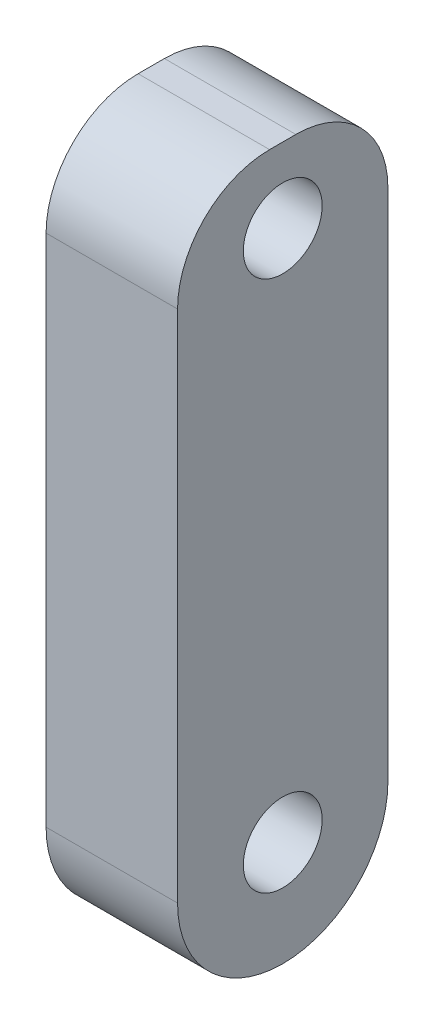
SolidWorks part; units mm, degrees
ref_plane "Front Plane" through (0, 0, 0) normal (0, 0, 1) x (1, 0, 0)
ref_plane "Top Plane" through (0, 0, 0) normal (0, 1, 0) x (1, 0, 0)
ref_plane "Right Plane" through (0, 0, 0) normal (1, 0, 0) x (0, 0, -1)
sketch "Sketch1" plane through (0, 0, 0) normal (1, 0, 0) x (0, 0, -1)
  line L0 (-21.5485, -38.9001) -> (108.4515, -38.9001) construction
  line L1 (44.1626, 9.8261) -> (44.1626, 29.3921)
  line L2 (47.6626, 32.8921) -> (48.6626, 32.8921)
  line L3 (52.1626, 29.3921) -> (52.1626, 9.8261)
  circle A0 centre (48.1626, 9.8261) radius 1.5
  circle A1 centre (48.1626, 9.8261) radius 4
  circle A2 centre (48.1626, 30.0515) radius 1.5
  arc A3 (52.1626, 29.3921) -> (48.6626, 32.8921) centre (48.6626, 29.3921) ccw
  arc A4 (44.1626, 29.3921) -> (47.6626, 32.8921) centre (47.6626, 29.3921) cw
  dimension "D2" = 3
  dimension "D3" = 8
  dimension "D4" = 3
  dimension "D5" = 3.5
  dimension "D1" = 130
extrude "Boss-Extrude1" add sketch "Sketch1" along normal blind 5 contours A1 A0 | A1 L3 L2 L1 A2
